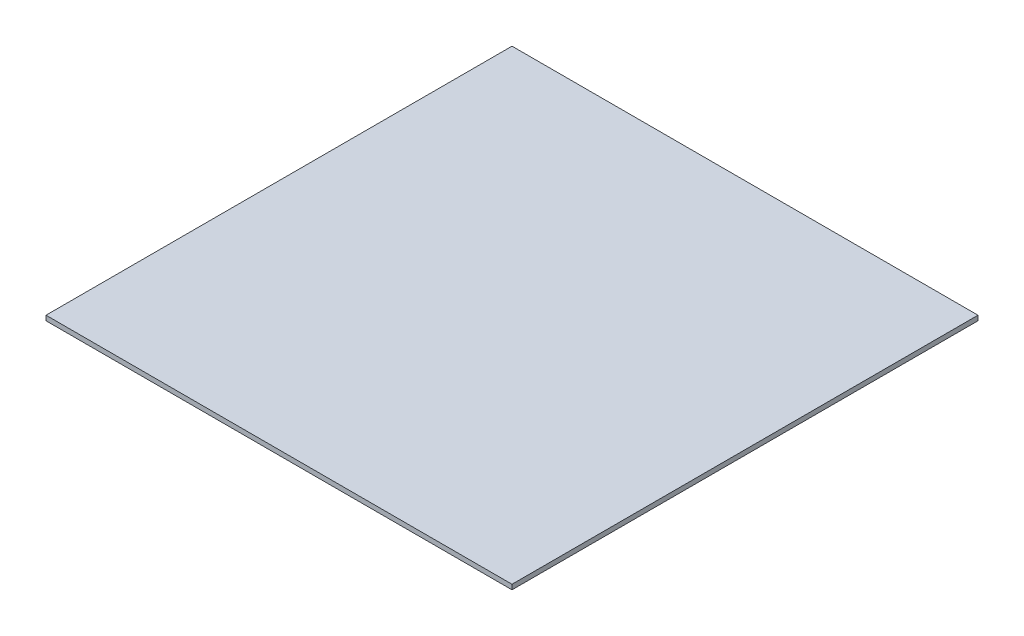
SolidWorks part; units mm, degrees
material "Oak"
ref_plane "Front" through (0, 0, 0) normal (0, 0, 1) x (1, 0, 0)
ref_plane "Top" through (0, 0, 0) normal (0, 1, 0) x (1, 0, 0)
ref_plane "Right" through (0, 0, 0) normal (1, 0, 0) x (0, 0, -1)
sketch "Sketch1" plane through (0, 0, 0) normal (0, 1, 0) x (1, 0, 0)
  line L1 (-304.8, 304.8) -> (304.8, 304.8)
  line L2 (-304.8, 304.8) -> (-304.8, -304.8)
  line L3 (-304.8, -304.8) -> (304.8, -304.8)
  line L4 (304.8, 304.8) -> (304.8, -304.8)
  point P4 (0, 304.8)
  point P6 (304.8, 0)
  dimension "D1" = 609.6
  dimension "D2" = 609.6
extrude "Boss-Extrude1" add sketch "Sketch1" along normal blind 6.35
sketch "Sketch2" plane through (0, 6.35, 0) normal (0, 1, 0) x (1, 0, 0)
  line L0 (-304.8, -304.8) -> (304.8, -304.8) construction
  line L1 (-203.2, 101.6) -> (203.2, 101.6)
  line L2 (-203.2, 101.6) -> (-203.2, -304.8)
  line L3 (-203.2, -304.8) -> (203.2, -304.8)
  line L4 (203.2, 101.6) -> (203.2, -304.8)
  point P6 (0, -304.8)
  point P7 (0, -304.8)
  dimension "D1" = 406.4
  dimension "D2" = 406.4
